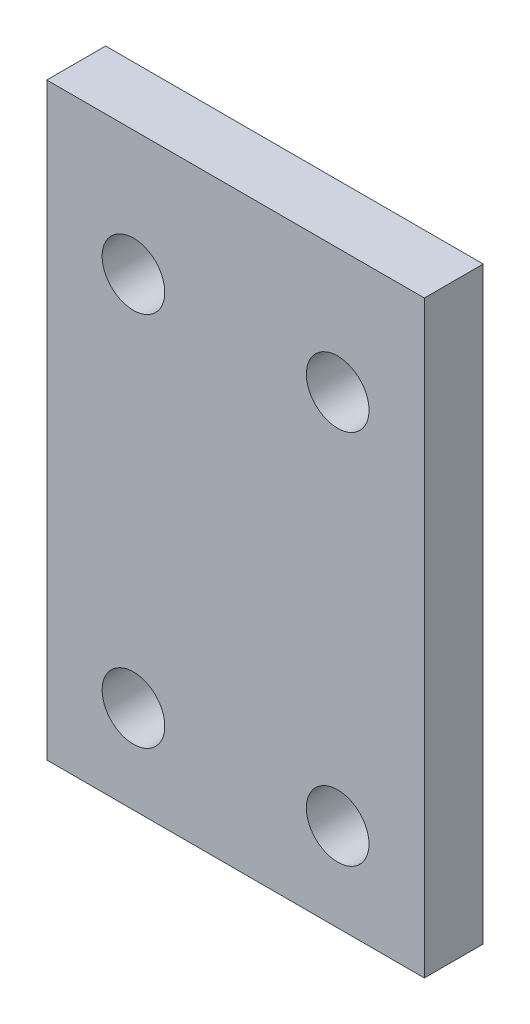
SolidWorks part; units mm, degrees
ref_plane "Front Plane" through (0, 0, 0) normal (0, 0, 1) x (1, 0, 0)
ref_plane "Top Plane" through (0, 0, 0) normal (0, 1, 0) x (1, 0, 0)
ref_plane "Right Plane" through (0, 0, 0) normal (1, 0, 0) x (0, 0, -1)
sketch "Sketch2" plane through (0, 0, 0) normal (0, 0, 1) x (1, 0, 0)
  line L0 (0, -1000) -> (0, 49000) construction
  line L1 (-20.3581, -31.75) -> (20.3581, -31.75)
  line L2 (-20.3581, -31.75) -> (-20.3581, 31.75)
  line L3 (-20.3581, 31.75) -> (20.3581, 31.75)
  line L4 (20.3581, -31.75) -> (20.3581, 31.75)
  line L5 (-20.3581, -31.75) -> (20.3581, 31.75) construction
  line L6 (-20.3581, 31.75) -> (20.3581, -31.75) construction
  circle A0 centre (11.0109, 18.288) radius 3.3782
  circle A1 centre (11.0109, -22.225) radius 3.3782
  circle A2 centre (-11.0109, -22.225) radius 3.3782
  circle A3 centre (-11.0109, 18.288) radius 3.3782
  point P0 (0, 0)
  dimension "D6" = 6.7564
  dimension "D1" = 40.7162
  dimension "D2" = 63.5
  dimension "D3" = 13.462
  dimension "D4" = 9.525
  dimension "D5" = 9.3472
extrude "Boss-Extrude1" add sketch "Sketch2" along normal blind 6.35
